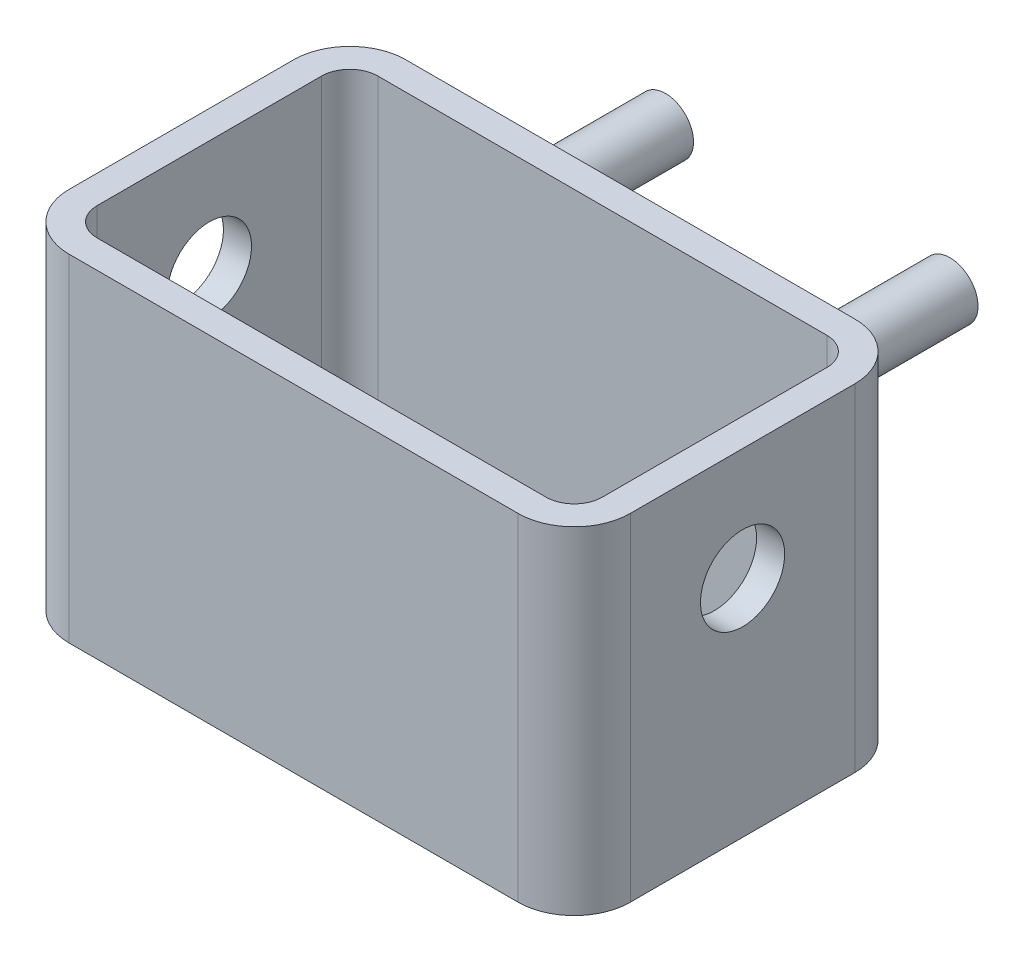
SolidWorks part; units mm, degrees
ref_plane "Přední rovina" through (0, 0, 0) normal (0, 0, 1) x (1, 0, 0)
ref_plane "Horní rovina" through (0, 0, 0) normal (0, 1, 0) x (1, 0, 0)
ref_plane "Pravá rovina" through (0, 0, 0) normal (1, 0, 0) x (0, 0, -1)
sketch "Skica1" plane through (0, 0, 0) normal (0, 0, 1) x (1, 0, 0)
  line L1 (0, 0) -> (100, 0)
  line L2 (0, 0) -> (0, 60)
  line L3 (0, 60) -> (100, 60)
  line L4 (100, 0) -> (100, 60)
  dimension "D1" = 100
  dimension "D2" = 60
extrude "Vysunout1" add sketch "Skica1" along normal blind 60
fillet "Zaoblit1" radius 10 4 edges at (0, 30, 0) (100, 30, 0) (100, 30, 60) (0, 30, 60)
shell "Skořepina1" thickness 5
sketch "Skica2" plane through (100, 0, 0) normal (1, 0, 0) x (0, 0, -1)
  line L0 (-30, 60) -> (-30, 0) construction
  line L1 (-50, 60) -> (-10, 60) construction
  line L2 (-50, 0) -> (-10, 0) construction
  circle A0 centre (-30, 40) radius 7.5
  dimension "D1" = 15
  dimension "D2" = 20
extrude "Odebrat vysunutím2" cut sketch "Skica2" against normal through all
sketch "Skica3" plane through (0, 0, 0) normal (0, 0, -1) x (-1, 0, 0)
  circle A0 centre (-76.959, 42.9423) radius 5
  circle A1 centre (-26.2643, 42.9423) radius 5
  dimension "D1" = 10
  dimension "D2" = 10
extrude "Vysunout2" add sketch "Skica3" along normal blind 30
